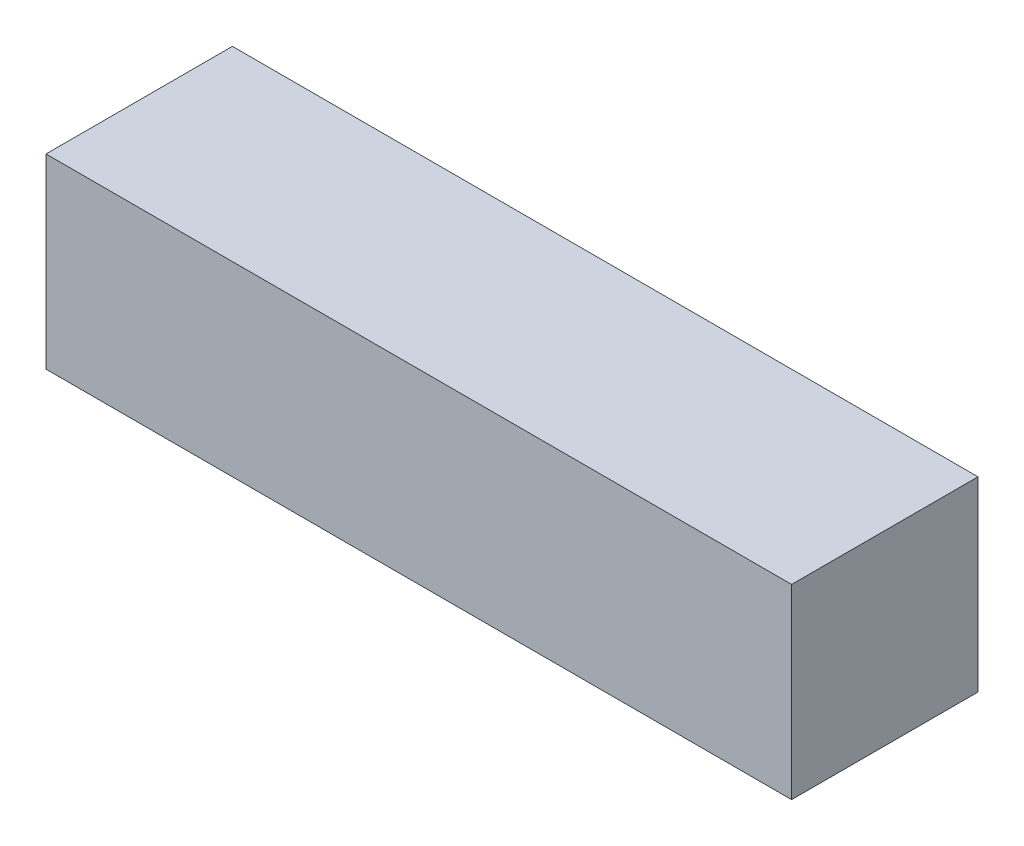
SolidWorks part; units mm, degrees
ref_plane "Front Plane" through (0, 0, 0) normal (0, 0, 1) x (1, 0, 0)
ref_plane "Top Plane" through (0, 0, 0) normal (0, 1, 0) x (1, 0, 0)
ref_plane "Right Plane" through (0, 0, 0) normal (1, 0, 0) x (0, 0, -1)
sketch "Sketch2" plane through (0, 0, 0) normal (1, 0, 0) x (0, 0, -1)
  line L0 (-1.5875, -1.5875) -> (1.5875, 1.5875) construction
  line L1 (-1.5875, 1.5875) -> (1.5875, 1.5875) construction
  line L2 (-1.5875, 1.5875) -> (-1.5875, -1.5875) construction
  line L3 (-1.5875, -1.5875) -> (1.5875, -1.5875) construction
  line L4 (1.5875, 1.5875) -> (1.5875, -1.5875) construction
  dimension "Height" = 3.175
  dimension "Width" = 3.175
sketch "Sketch1" plane through (0, 0, 0) normal (0, 0, 1) x (1, 0, 0)
  line L0 (-6.35, 0) -> (6.35, 0) construction
  line L1 (-6.35, 1.5875) -> (6.35, 1.5875) construction
  point P8 (0, 0)
  dimension "Length" = 12.7
sketch "Sketch3" plane through (0, 0, 0) normal (0, 1, 0) x (1, 0, 0)
  line L1 (-6.35, 1.5875) -> (6.35, 1.5875)
  line L2 (-6.35, 1.5875) -> (-6.35, -1.5875)
  line L3 (-6.35, -1.5875) -> (6.35, -1.5875)
  line L4 (6.35, 1.5875) -> (6.35, -1.5875)
extrude "Extrude1" add sketch "Sketch3" against normal up to vertex (1.5875 mm away) and the other way up to vertex (1.5875 mm away)
sketch "Sketch5" plane through (0, 0, 0) normal (0, 0, 1) x (1, 0, 0)
  line L0 (6.35, 0) -> (2.1167, 0) construction
  line L1 (2.1167, 0) -> (-2.1167, 0) construction
  line L2 (-2.1167, 0) -> (2.1167, 0) construction
  line L3 (2.1167, 0) -> (-2.1167, 0) construction
  line L4 (-2.1167, 0) -> (-6.35, 0) construction
  point P2 (-4.2333, 0)
  point P7 (0, 0)
  point P8 (4.2333, 0)
  point P9 (-2.1167, 0)
  point P10 (-6.35, 0)
  point P11 (2.1167, 0)
  point P13 (6.35, 0)
sketch "Sketch6" plane through (0, 0, 1.5875) normal (0, 0, 1) x (1, 0, 0)
  line L1 (-2.1167, 0) -> (-6.35, 0) construction
  line L2 (2.1167, 0) -> (-2.1167, 0) construction
  line L3 (6.35, 0) -> (2.1167, 0) construction
  point P0 (-4.2333, 0)
  point P1 (-2.1167, 0)
  point P4 (0, 0)
  point P5 (2.1167, 0)
  point P6 (4.2333, 0)
